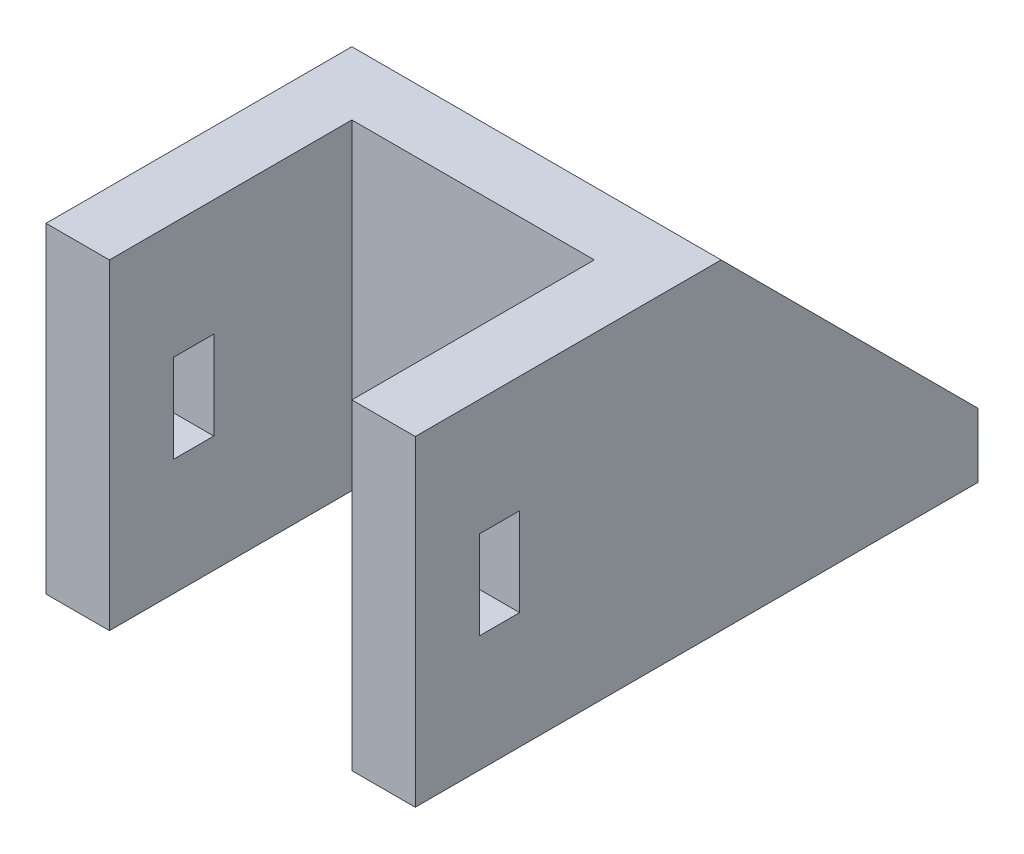
SolidWorks part; units mm, degrees
ref_plane "前视基准面" through (0, 0, 0) normal (0, 0, 1) x (1, 0, 0)
ref_plane "上视基准面" through (0, 0, 0) normal (0, 1, 0) x (1, 0, 0)
ref_plane "右视基准面" through (0, 0, 0) normal (1, 0, 0) x (0, 0, -1)
sketch "草图1" plane through (0, 0, 0) normal (0, 1, 0) x (1, 0, 0)
  line L0 (-4.794, 11.1468) -> (-4.794, -7.9032)
  line L1 (-4.794, 27.1468) -> (18.206, 27.1468)
  line L2 (-4.794, 27.1468) -> (-4.794, 11.1468)
  line L3 (-0.844, 7.1968) -> (14.256, 7.1968)
  line L4 (18.206, 27.1468) -> (18.206, 11.1468)
  line L6 (-0.844, 7.1968) -> (-0.844, -7.9032)
  line L10 (14.256, 7.1968) -> (14.256, -7.9032)
  line L15 (-0.844, -7.9032) -> (-4.794, -7.9032)
  line L19 (14.256, -7.9032) -> (18.206, -7.9032)
  line L21 (18.206, 11.1468) -> (18.206, -7.9032)
  dimension "D1" = 16
  dimension "D2" = 3.95
  dimension "D3" = 3.95
  dimension "D4" = 23
extrude "凸台-拉伸1" add sketch "草图1" along normal blind 4
sketch "草图2" plane through (0, 4, 0) normal (0, 1, 0) x (1, 0, 0)
  line L1 (-4.794, 11.1468) -> (-0.844, 11.1468)
  line L2 (-4.794, 11.1468) -> (-4.794, -7.9032)
  line L3 (-4.794, -7.9032) -> (-0.844, -7.9032)
  line L4 (-0.844, 7.1968) -> (-0.844, -7.9032)
  line L5 (18.206, 11.1468) -> (14.256, 11.1468)
  line L6 (18.206, 11.1468) -> (18.206, -7.9032)
  line L7 (18.206, -7.9032) -> (14.256, -7.9032)
  line L8 (14.256, 7.1968) -> (14.256, -7.9032)
  line L9 (14.256, 11.1468) -> (-0.844, 11.1468)
  line L11 (14.256, 7.1968) -> (-0.844, 7.1968)
  dimension "D1" = 19.05
  dimension "D2" = 19.05
extrude "凸台-拉伸2" add sketch "草图2" along normal blind 16
sketch "草图3" plane through (-4.794, 0, 0) normal (-1, 0, 0) x (0, 0, 1)
  line L0 (-11.1468, 20) -> (-27.1468, 4)
  line L1 (-27.1468, 4) -> (-11.1468, 4)
  line L2 (-11.1468, 4) -> (-11.1468, 20)
extrude "凸台-拉伸3" add sketch "草图3" against normal blind 4 separate body
sketch "草图4" plane through (18.206, 0, 0) normal (1, 0, 0) x (0, 0, -1)
  line L0 (11.1468, 20) -> (11.1468, 4)
  line L1 (11.1468, 4) -> (27.1468, 4)
  line L2 (27.1468, 4) -> (11.1468, 20)
extrude "凸台-拉伸4" add sketch "草图4" against normal blind 4
sketch "草图5" plane through (18.206, 0, 0) normal (1, 0, 0) x (0, 0, -1)
  line L0 (-7.9032, 20) -> (-7.9032, 0) construction
  line L1 (-3.9032, 12.75) -> (-1.4032, 12.75)
  line L2 (-3.9032, 12.75) -> (-3.9032, 7.25)
  line L3 (-3.9032, 7.25) -> (-1.4032, 7.25)
  line L4 (-1.4032, 12.75) -> (-1.4032, 7.25)
  line L5 (-7.9032, 20) -> (11.1468, 20) construction
  point P6 (-3.9032, 10)
  point P11 (-4.5365, 2.5349)
  dimension "D1" = 5.5
  dimension "D2" = 2.5
  dimension "D3" = 4
  dimension "D4" = 10
extrude "切除-拉伸1" cut sketch "草图5" against normal blind 32
